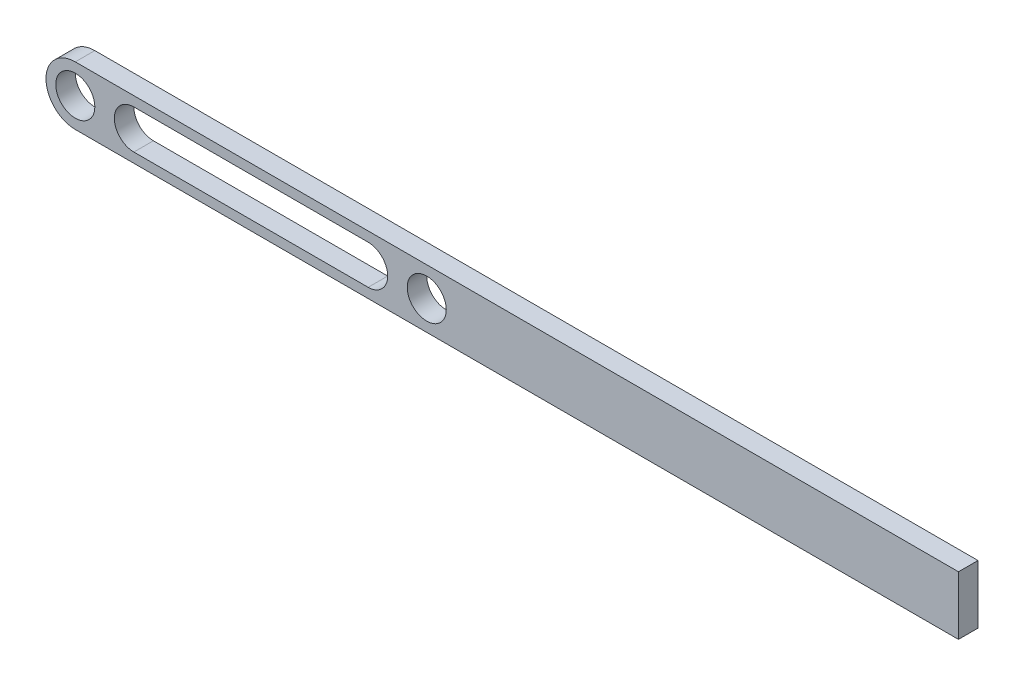
SolidWorks part; units mm, degrees
ref_plane "Front Plane" through (0, 0, 0) normal (0, 0, 1) x (1, 0, 0)
ref_plane "Top Plane" through (0, 0, 0) normal (0, 1, 0) x (1, 0, 0)
ref_plane "Right Plane" through (0, 0, 0) normal (1, 0, 0) x (0, 0, -1)
sketch "Sketch1" plane through (0, 0, 0) normal (0, 0, 1) x (1, 0, 0)
  line L0 (0, 0) -> (180, 0) construction
  line L1 (30, 10) -> (150, 10)
  line L2 (30, -10) -> (150, -10)
  line L3 (0, 15) -> (180, 15)
  line L4 (0, -15) -> (180, -15)
  line L6 (180, 15) -> (452.335, 15)
  line L8 (180, -15) -> (452.335, -15)
  line L9 (452.335, 15) -> (452.335, -15)
  arc A2 (0, 15) -> (0, -15) centre (0, 0) ccw
  arc A5 (30, 10) -> (30, -10) centre (30, 0) ccw
  arc A7 (150, -10) -> (150, 10) centre (150, 0) ccw
  circle A8 centre (0, 0) radius 10
  circle A9 centre (180, 0) radius 10
  dimension "D1" = 20
  dimension "D2" = 20
  dimension "D5" = 180
  dimension "D6" = 30
  dimension "D7" = 30
extrude "Boss-Extrude1" add sketch "Sketch1" along normal blind 10
